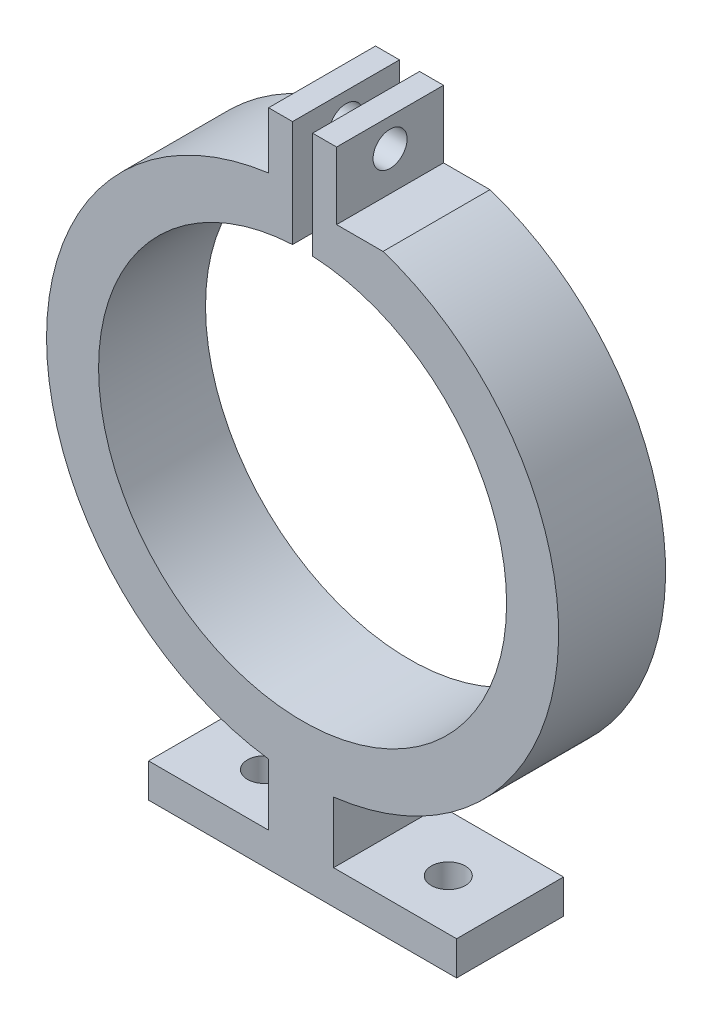
SolidWorks part; units mm, degrees
ref_plane "Front Plane" through (0, 0, 0) normal (0, 0, 1) x (1, 0, 0)
ref_plane "Top Plane" through (0, 0, 0) normal (0, 1, 0) x (1, 0, 0)
ref_plane "Right Plane" through (0, 0, 0) normal (1, 0, 0) x (0, 0, -1)
sketch "Sketch2" plane through (0, 0, 0) normal (0, 0, 1) x (1, 0, 0)
  line L0 (0, 29.0113) -> (0, -32.6661) construction
  line L1 (14.4009, -32.6661) -> (-14.4009, -32.6661)
  line L2 (-14.4009, -32.6661) -> (-14.4009, -29.4861)
  line L3 (-14.4009, -29.4861) -> (-3.18, -29.4861)
  line L5 (-3.18, 23.7279) -> (-3.18, 29.0113)
  line L6 (-3.18, 29.0113) -> (3.18, 29.0113)
  line L7 (14.4009, -32.6661) -> (14.4009, -29.4861)
  line L8 (14.4009, -29.4861) -> (2.8996, -29.4861)
  line L10 (3.18, 23.7279) -> (3.18, 29.0113)
  line L11 (-3.18, -23.7279) -> (-3.18, -29.4861)
  line L13 (2.8996, -23.7638) -> (2.8996, -29.4861)
  arc A0 (-3.18, -23.7279) -> (-3.18, 23.7279) centre (0, 0) cw
  arc A1 (2.8996, -23.7638) -> (3.18, 23.7279) centre (0, 0) ccw
  point P1 (0, -17.0437)
  point P6 (0, 0)
  point P9 (2.8996, -13.8637)
  point P14 (-3.18, 29.0113)
  dimension "D1" = 23.94
  dimension "D2" = 3.18
  dimension "D3" = 3.18
extrude "Boss-Extrude1" add sketch "Sketch2" along normal blind 10
sketch "Sketch3" plane through (0, 0, 10) normal (0, 0, 1) x (1, 0, 0)
  circle A0 centre (0, 0) radius 19.075
  point P2 (0, 0)
  dimension "D1" = 38.15
extrude "Cut-Extrude1" cut sketch "Sketch3" against normal through all
sketch "Sketch4" plane through (0, 0, 10) normal (0, 0, 1) x (1, 0, 0)
  line L0 (3.18, 29.0113) -> (-3.18, 29.0113) construction
  line L1 (-0.9385, 29.0113) -> (0.9385, 29.0113)
  line L2 (-0.9385, 29.0113) -> (-0.9385, 19.0519)
  line L3 (-0.9385, 19.0519) -> (0.9385, 19.0519)
  line L4 (0.9385, 29.0113) -> (0.9385, 19.0519)
  line L5 (0, 0) -> (0, 12.768) construction
  circle A0 centre (0, 0) radius 19.075 construction
extrude "Cut-Extrude2" cut sketch "Sketch4" against normal through all
sketch "Sketch5" plane through (3.18, 0, 0) normal (1, 0, 0) x (0, 0, -1)
  line L0 (-10, 29.0113) -> (0, 29.0113) construction
  line L3 (-5, 29.0113) -> (-5, 23.7279) construction
  line L4 (-10, 23.7279) -> (0, 23.7279) construction
  circle A0 centre (-5, 26.3696) radius 1.59
  point P4 (-5, 26.3696)
  dimension "D1" = 3.18
extrude "Cut-Extrude3" cut sketch "Sketch5" against normal blind 10
sketch "Sketch6" plane through (0, -29.4861, 0) normal (0, 1, 0) x (1, 0, 0)
  circle A0 centre (8.9126, -5.2898) radius 1.59
  circle A1 centre (-8.2735, -5.2898) radius 1.59
  dimension "D1" = 3.18
  dimension "D2" = 3.18
extrude "Cut-Extrude4" cut sketch "Sketch6" against normal blind 10
sketch "Sketch7" plane through (3.18, 0, 0) normal (1, 0, 0) x (0, 0, -1)
  line L0 (-10, 23.7279) -> (-10, 29.0113) construction
  line L1 (-10, 23.7279) -> (0, 23.7279)
  line L2 (-10, 23.7279) -> (-10, 22.7279)
  line L3 (-10, 22.7279) -> (0, 22.7279)
  line L4 (0, 23.7279) -> (0, 22.7279)
  line L5 (-10, 23.7279) -> (0, 23.7279) construction
  line L6 (0, 23.7279) -> (0, 29.0113) construction
  dimension "D1" = 1
extrude "Cut-Extrude5" cut sketch "Sketch7" along normal blind 29.718 contours L2 L3 L4 L1
